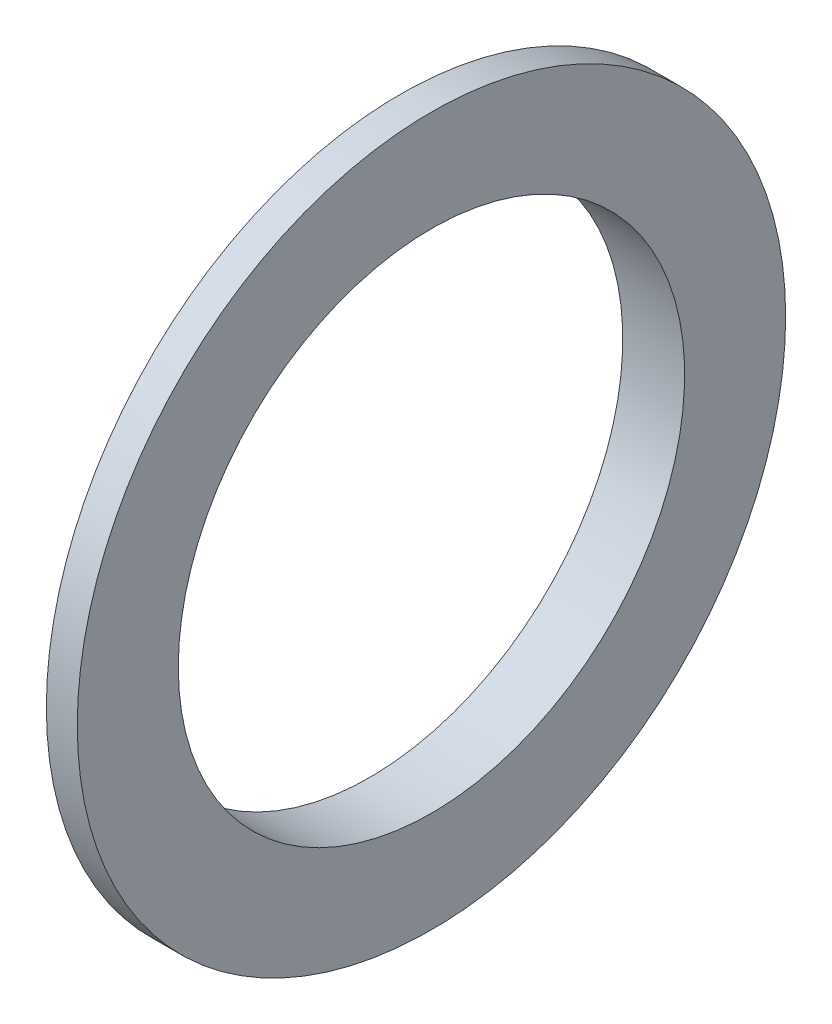
SolidWorks part; units mm, degrees
ref_plane "Front Plane" through (0, 0, 0) normal (0, 0, 1) x (1, 0, 0)
ref_plane "Top Plane" through (0, 0, 0) normal (0, 1, 0) x (1, 0, 0)
ref_plane "Right Plane" through (0, 0, 0) normal (1, 0, 0) x (0, 0, -1)
sketch "Sketch1" plane through (0, 0, 0) normal (0, 1, 0) x (1, 0, 0)
  line L0 (-8.7351, 16.2331) -> (-8.7351, 8.7479)
  line L1 (-8.7351, 8.7479) -> (0, 8.7479)
  line L2 (0, 8.7479) -> (0, 23.0069)
  line L3 (-8.7351, 16.2331) -> (-4.3675, 16.2331)
  line L4 (-4.3675, 16.2331) -> (-4.3675, 23.0069)
  line L5 (-4.3675, 23.0069) -> (0, 23.0069)
  line L6 (-12.0675, -26.9931) -> (3.181, -26.9931) construction
  dimension "D1" = 50
revolve "Revolve1" add sketch "Sketch1" angle 360 about L6
